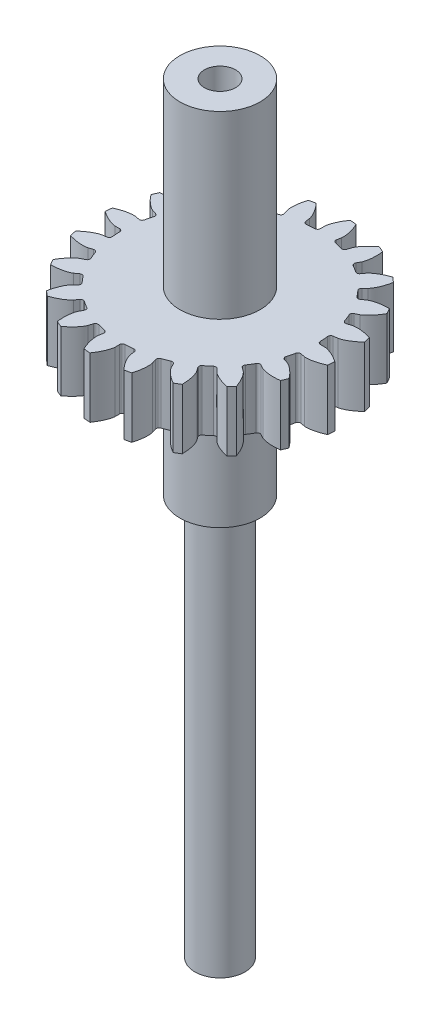
SolidWorks part; units mm, degrees
ref_plane "Front Plane" through (0, 0, 0) normal (0, 0, 1) x (1, 0, 0)
ref_plane "Top Plane" through (0, 0, 0) normal (0, 1, 0) x (1, 0, 0)
ref_plane "Right Plane" through (0, 0, 0) normal (1, 0, 0) x (0, 0, -1)
sketch "Sketch1" plane through (0, 0, 0) normal (0, 1, 0) x (1, 0, 0)
  circle A0 centre (0, 0) radius 2.5
  dimension "D1" = 5
extrude "BearingSection" add sketch "Sketch1" along normal mid plane 5
sketch "Sketch2" plane through (0, 2.5, 0) normal (0, 1, 0) x (1, 0, 0)
  circle A0 centre (0, 0) radius 4
  dimension "D1" = 8
extrude "Boss-Extrude2" add sketch "Sketch2" along normal blind 12
ref_plane "GearPlane" through (0, 14.5, 0) normal (0, 1, 0) x (1, 0, 0)
sketch "GearSketch" plane through (0, 14.5, 0) normal (0, 1, 0) x (1, 0, 0)
  line L122 (-9.8507, 1.7712) -> (-10.2891, 1.85)
  line L123 (-10.4541, 0) -> (-10.0086, 0)
  line L124 (-9.9159, -1.3596) -> (-10.3572, -1.4201)
  line L125 (-9.9424, -3.2305) -> (-9.5188, -3.0928)
  line L126 (-9.0104, -4.3572) -> (-9.4114, -4.5511)
  line L127 (-8.4575, -6.1448) -> (-8.0972, -5.8829)
  line L128 (-7.223, -6.9283) -> (-7.5444, -7.2367)
  line L129 (-6.1448, -8.4575) -> (-5.8829, -8.0972)
  line L130 (-4.7285, -8.8212) -> (-4.9389, -9.2138)
  line L131 (-3.2305, -9.9424) -> (-3.0928, -9.5188)
  line L132 (-1.7712, -9.8507) -> (-1.85, -10.2891)
  line L133 (0, -10.4541) -> (0, -10.0086)
  line L134 (1.3596, -9.9159) -> (1.4201, -10.3572)
  line L135 (3.2305, -9.9424) -> (3.0928, -9.5188)
  line L136 (4.3572, -9.0104) -> (4.5511, -9.4114)
  line L137 (6.1448, -8.4575) -> (5.8829, -8.0972)
  line L138 (6.9283, -7.223) -> (7.2367, -7.5444)
  line L139 (8.4575, -6.1448) -> (8.0972, -5.8829)
  line L140 (8.8212, -4.7285) -> (9.2138, -4.9389)
  line L141 (9.9424, -3.2305) -> (9.5188, -3.0928)
  line L142 (9.8507, -1.7712) -> (10.2891, -1.85)
  line L143 (10.4541, 0) -> (10.0086, 0)
  line L144 (9.9159, 1.3596) -> (10.3572, 1.4201)
  line L145 (9.9424, 3.2305) -> (9.5188, 3.0928)
  line L146 (9.0104, 4.3572) -> (9.4114, 4.5511)
  line L147 (8.4575, 6.1448) -> (8.0972, 5.8829)
  line L148 (7.223, 6.9283) -> (7.5444, 7.2367)
  line L149 (6.1448, 8.4575) -> (5.8829, 8.0972)
  line L150 (4.7285, 8.8212) -> (4.9389, 9.2138)
  line L151 (3.2305, 9.9424) -> (3.0928, 9.5188)
  line L152 (1.7712, 9.8507) -> (1.85, 10.2891)
  line L153 (0, 10.4541) -> (0, 10.0086)
  line L154 (-1.3596, 9.9159) -> (-1.4201, 10.3572)
  line L155 (-3.2305, 9.9424) -> (-3.0928, 9.5188)
  line L156 (-4.3572, 9.0104) -> (-4.5511, 9.4114)
  line L157 (-6.1448, 8.4575) -> (-5.8829, 8.0972)
  line L158 (-6.9283, 7.223) -> (-7.2367, 7.5444)
  line L159 (-8.4575, 6.1448) -> (-8.0972, 5.8829)
  line L160 (-8.8212, 4.7285) -> (-9.2138, 4.9389)
  line L161 (-9.9424, 3.2305) -> (-9.5188, 3.0928)
  arc A240 (-9.3379, 2.7498) -> (-9.5292, 1.9881) centre (0, 0) ccw
  arc A241 (-9.8507, 1.7712) -> (-9.5292, 1.9881) centre (-9.8015, 2.0449) ccw
  arc A242 (-12.1552, 1.4168) -> (-12.2141, 0.7565) centre (0, 0) ccw
  arc A243 (-9.7306, -0.2704) -> (-10.0086, 0) centre (-10.0086, -0.2781) ccw
  arc A244 (-9.7306, -0.2704) -> (-9.6772, -1.0539) centre (0, 0) ccw
  arc A245 (-9.9159, -1.3596) -> (-9.6772, -1.0539) centre (-9.9536, -1.084) ccw
  arc A246 (-11.9981, -2.4087) -> (-11.8501, -3.0549) centre (0, 0) ccw
  arc A247 (-9.1708, -3.2641) -> (-9.5188, -3.0928) centre (-9.4328, -3.3574) ccw
  arc A248 (-9.1708, -3.2641) -> (-8.8778, -3.9927) centre (0, 0) ccw
  arc A249 (-9.0104, -4.3572) -> (-8.8778, -3.9927) centre (-9.1315, -4.1068) ccw
  arc A250 (-10.6666, -5.9984) -> (-10.3261, -6.5672) centre (0, 0) ccw
  arc A251 (-7.7133, -5.9383) -> (-8.0972, -5.8829) centre (-7.9337, -6.1079) ccw
  arc A252 (-7.7133, -5.9383) -> (-7.2095, -6.5407) centre (0, 0) ccw
  arc A253 (-7.223, -6.9283) -> (-7.2095, -6.5407) centre (-7.4155, -6.7276) ccw
  arc A254 (-8.2909, -9.001) -> (-7.7913, -9.4367) centre (0, 0) ccw
  arc A255 (-5.5008, -8.0312) -> (-5.8829, -8.0972) centre (-5.6579, -8.2606) ccw
  arc A256 (-5.5008, -8.0312) -> (-4.8355, -8.4485) centre (0, 0) ccw
  arc A257 (-4.7285, -8.8212) -> (-4.8355, -8.4485) centre (-4.9736, -8.6898) ccw
  arc A258 (-5.1037, -11.1225) -> (-4.4939, -11.3825) centre (0, 0) ccw
  arc A259 (-2.7498, -9.3379) -> (-3.0928, -9.5188) centre (-2.8283, -9.6047) ccw
  arc A260 (-2.7498, -9.3379) -> (-1.9881, -9.5292) centre (0, 0) ccw
  arc A261 (-1.7712, -9.8507) -> (-1.9881, -9.5292) centre (-2.0449, -9.8015) ccw
  arc A262 (-1.4168, -12.1552) -> (-0.7565, -12.2141) centre (0, 0) ccw
  arc A263 (0.2704, -9.7306) -> (0, -10.0086) centre (0.2781, -10.0086) ccw
  arc A264 (0.2704, -9.7306) -> (1.0539, -9.6772) centre (0, 0) ccw
  arc A265 (1.3596, -9.9159) -> (1.0539, -9.6772) centre (1.084, -9.9536) ccw
  arc A266 (2.4087, -11.9981) -> (3.0549, -11.8501) centre (0, 0) ccw
  arc A267 (3.2641, -9.1708) -> (3.0928, -9.5188) centre (3.3574, -9.4328) ccw
  arc A268 (3.2641, -9.1708) -> (3.9927, -8.8778) centre (0, 0) ccw
  arc A269 (4.3572, -9.0104) -> (3.9927, -8.8778) centre (4.1068, -9.1315) ccw
  arc A270 (5.9984, -10.6666) -> (6.5672, -10.3261) centre (0, 0) ccw
  arc A271 (5.9383, -7.7133) -> (5.8829, -8.0972) centre (6.1079, -7.9337) ccw
  arc A272 (5.9383, -7.7133) -> (6.5407, -7.2095) centre (0, 0) ccw
  arc A273 (6.9283, -7.223) -> (6.5407, -7.2095) centre (6.7276, -7.4155) ccw
  arc A274 (9.001, -8.2909) -> (9.4367, -7.7913) centre (0, 0) ccw
  arc A275 (8.0312, -5.5008) -> (8.0972, -5.8829) centre (8.2606, -5.6579) ccw
  arc A276 (8.0312, -5.5008) -> (8.4485, -4.8355) centre (0, 0) ccw
  arc A277 (8.8212, -4.7285) -> (8.4485, -4.8355) centre (8.6898, -4.9736) ccw
  arc A278 (11.1225, -5.1037) -> (11.3825, -4.4939) centre (0, 0) ccw
  arc A279 (9.3379, -2.7498) -> (9.5188, -3.0928) centre (9.6047, -2.8283) ccw
  arc A280 (9.3379, -2.7498) -> (9.5292, -1.9881) centre (0, 0) ccw
  arc A281 (9.8507, -1.7712) -> (9.5292, -1.9881) centre (9.8015, -2.0449) ccw
  arc A282 (12.1552, -1.4168) -> (12.2141, -0.7565) centre (0, 0) ccw
  arc A283 (9.7306, 0.2704) -> (10.0086, 0) centre (10.0086, 0.2781) ccw
  arc A284 (9.7306, 0.2704) -> (9.6772, 1.0539) centre (0, 0) ccw
  arc A285 (9.9159, 1.3596) -> (9.6772, 1.0539) centre (9.9536, 1.084) ccw
  arc A286 (11.9981, 2.4087) -> (11.8501, 3.0549) centre (0, 0) ccw
  arc A287 (9.1708, 3.2641) -> (9.5188, 3.0928) centre (9.4328, 3.3574) ccw
  arc A288 (9.1708, 3.2641) -> (8.8778, 3.9927) centre (0, 0) ccw
  arc A289 (9.0104, 4.3572) -> (8.8778, 3.9927) centre (9.1315, 4.1068) ccw
  arc A290 (10.6666, 5.9984) -> (10.3261, 6.5672) centre (0, 0) ccw
  arc A291 (7.7133, 5.9383) -> (8.0972, 5.8829) centre (7.9337, 6.1079) ccw
  arc A292 (7.7133, 5.9383) -> (7.2095, 6.5407) centre (0, 0) ccw
  arc A293 (7.223, 6.9283) -> (7.2095, 6.5407) centre (7.4155, 6.7276) ccw
  arc A294 (8.2909, 9.001) -> (7.7913, 9.4367) centre (0, 0) ccw
  arc A295 (5.5008, 8.0312) -> (5.8829, 8.0972) centre (5.6579, 8.2606) ccw
  arc A296 (5.5008, 8.0312) -> (4.8355, 8.4485) centre (0, 0) ccw
  arc A297 (4.7285, 8.8212) -> (4.8355, 8.4485) centre (4.9736, 8.6898) ccw
  arc A298 (5.1037, 11.1225) -> (4.4939, 11.3825) centre (0, 0) ccw
  arc A299 (2.7498, 9.3379) -> (3.0928, 9.5188) centre (2.8283, 9.6047) ccw
  arc A300 (2.7498, 9.3379) -> (1.9881, 9.5292) centre (0, 0) ccw
  arc A301 (1.7712, 9.8507) -> (1.9881, 9.5292) centre (2.0449, 9.8015) ccw
  arc A302 (1.4168, 12.1552) -> (0.7565, 12.2141) centre (0, 0) ccw
  arc A303 (-0.2704, 9.7306) -> (0, 10.0086) centre (-0.2781, 10.0086) ccw
  arc A304 (-0.2704, 9.7306) -> (-1.0539, 9.6772) centre (0, 0) ccw
  arc A305 (-1.3596, 9.9159) -> (-1.0539, 9.6772) centre (-1.084, 9.9536) ccw
  arc A306 (-2.4087, 11.9981) -> (-3.0549, 11.8501) centre (0, 0) ccw
  arc A307 (-3.2641, 9.1708) -> (-3.0928, 9.5188) centre (-3.3574, 9.4328) ccw
  arc A308 (-3.2641, 9.1708) -> (-3.9927, 8.8778) centre (0, 0) ccw
  arc A309 (-4.3572, 9.0104) -> (-3.9927, 8.8778) centre (-4.1068, 9.1315) ccw
  arc A310 (-5.9984, 10.6666) -> (-6.5672, 10.3261) centre (0, 0) ccw
  arc A311 (-5.9383, 7.7133) -> (-5.8829, 8.0972) centre (-6.1079, 7.9337) ccw
  arc A312 (-5.9383, 7.7133) -> (-6.5407, 7.2095) centre (0, 0) ccw
  arc A313 (-6.9283, 7.223) -> (-6.5407, 7.2095) centre (-6.7276, 7.4155) ccw
  arc A314 (-9.001, 8.2909) -> (-9.4367, 7.7913) centre (0, 0) ccw
  arc A315 (-8.0312, 5.5008) -> (-8.0972, 5.8829) centre (-8.2606, 5.6579) ccw
  arc A316 (-8.0312, 5.5008) -> (-8.4485, 4.8355) centre (0, 0) ccw
  arc A317 (-8.8212, 4.7285) -> (-8.4485, 4.8355) centre (-8.6898, 4.9736) ccw
  arc A318 (-11.1225, 5.1037) -> (-11.3825, 4.4939) centre (0, 0) ccw
  arc A319 (-9.3379, 2.7498) -> (-9.5188, 3.0928) centre (-9.6047, 2.8283) ccw
  spline S121 degree 4 poles (-10.2891, 1.85) (-10.2967, 1.8512) (-10.3182, 1.8541) (-10.3591, 1.8575) (-10.4261, 1.8604) (-10.5116, 1.8598) (-10.6222, 1.8543) (-10.7524, 1.8417) (-10.8951, 1.8213) (-11.0496, 1.7923) (-11.203, 1.7573) (-11.3551, 1.7168) (-11.5057, 1.6713) (-11.6868, 1.6104) (-11.8683, 1.5419) (-12.0112, 1.4818) (-12.1166, 1.4346) (-12.1552, 1.4168) knots 0 0 0 0 0 0.005377 0.015084 0.028532 0.04661 0.064855 0.092111 0.119476 0.146842 0.174209 0.201575 0.228941 0.256307 0.307035 0.336625 0.336625 0.336625 0.336625 0.336625
  spline S122 degree 4 poles (-12.2141, 0.7565) (-12.1792, 0.7322) (-12.0839, 0.6671) (-11.9538, 0.5827) (-11.7874, 0.4832) (-11.6199, 0.3911) (-11.4797, 0.3198) (-11.3372, 0.2529) (-11.1924, 0.1913) (-11.0454, 0.1354) (-10.9086, 0.0902) (-10.7827, 0.0547) (-10.6748, 0.0297) (-10.5907, 0.014) (-10.5243, 0.005) (-10.4835, 0.0011) (-10.4618, 0.0002) (-10.4541, 0) knots 0 0 0 0 0 0.02959 0.080317 0.107684 0.13505 0.162416 0.189782 0.217148 0.244514 0.27177 0.290014 0.308093 0.321541 0.331248 0.336625 0.336625 0.336625 0.336625 0.336625
  spline S123 degree 4 poles (-10.3572, -1.4201) (-10.3648, -1.4213) (-10.3861, -1.4252) (-10.4261, -1.4345) (-10.4907, -1.4525) (-10.5718, -1.4795) (-10.6753, -1.5189) (-10.7952, -1.5711) (-10.9246, -1.6346) (-11.0627, -1.7099) (-11.1977, -1.7906) (-11.3299, -1.8762) (-11.4591, -1.9659) (-11.6125, -2.0799) (-11.7639, -2.2011) (-11.8813, -2.3024) (-11.9668, -2.3799) (-11.9981, -2.4087) knots 0 0 0 0 0 0.005377 0.015084 0.028532 0.04661 0.064855 0.092111 0.119476 0.146842 0.174209 0.201575 0.228941 0.256307 0.307035 0.336625 0.336625 0.336625 0.336625 0.336625
  spline S124 degree 4 poles (-11.8501, -3.0549) (-11.8094, -3.0672) (-11.6986, -3.0997) (-11.5488, -3.1397) (-11.3598, -3.183) (-11.172, -3.2188) (-11.0167, -3.2433) (-10.8605, -3.2628) (-10.7037, -3.2767) (-10.5467, -3.2844) (-10.4025, -3.2852) (-10.2719, -3.28) (-10.1615, -3.2705) (-10.0767, -3.2594) (-10.0108, -3.2475) (-9.9707, -3.2385) (-9.9498, -3.2327) (-9.9424, -3.2305) knots 0 0 0 0 0 0.02959 0.080317 0.107684 0.13505 0.162416 0.189782 0.217148 0.244514 0.27177 0.290014 0.308093 0.321541 0.331248 0.336625 0.336625 0.336625 0.336625 0.336625
  spline S125 degree 4 poles (-9.4114, -4.5511) (-9.4183, -4.5546) (-9.4374, -4.5649) (-9.4725, -4.5861) (-9.5284, -4.6232) (-9.5972, -4.6739) (-9.6835, -4.7434) (-9.7814, -4.8302) (-9.8848, -4.9305) (-9.9928, -5.0448) (-10.0964, -5.1633) (-10.1956, -5.2855) (-10.2907, -5.4108) (-10.4014, -5.5665) (-10.5079, -5.7286) (-10.5883, -5.8612) (-10.6457, -5.9613) (-10.6666, -5.9984) knots 0 0 0 0 0 0.005377 0.015084 0.028532 0.04661 0.064855 0.092111 0.119476 0.146842 0.174209 0.201575 0.228941 0.256307 0.307035 0.336625 0.336625 0.336625 0.336625 0.336625
  spline S126 degree 4 poles (-10.3261, -6.5672) (-10.2836, -6.5664) (-10.1682, -6.5631) (-10.0134, -6.5549) (-9.8202, -6.5375) (-9.6306, -6.5136) (-9.4752, -6.4889) (-9.3206, -6.4592) (-9.1673, -6.4239) (-9.0155, -6.3828) (-8.8782, -6.3389) (-8.7555, -6.2937) (-8.6536, -6.2505) (-8.5763, -6.2137) (-8.5173, -6.182) (-8.482, -6.1611) (-8.4639, -6.1492) (-8.4575, -6.1448) knots 0 0 0 0 0 0.02959 0.080317 0.107684 0.13505 0.162416 0.189782 0.217148 0.244514 0.27177 0.290014 0.308093 0.321541 0.331248 0.336625 0.336625 0.336625 0.336625 0.336625
  spline S127 degree 4 poles (-7.5444, -7.2367) (-7.5499, -7.2421) (-7.5649, -7.2578) (-7.5917, -7.2889) (-7.6334, -7.3414) (-7.6832, -7.4109) (-7.7437, -7.5036) (-7.81, -7.6164) (-7.8774, -7.7437) (-7.9448, -7.8858) (-8.0067, -8.0305) (-8.0633, -8.1774) (-8.115, -8.3259) (-8.1722, -8.5083) (-8.2234, -8.6954) (-8.2589, -8.8463) (-8.2825, -8.9593) (-8.2909, -9.001) knots 0 0 0 0 0 0.005377 0.015084 0.028532 0.04661 0.064855 0.092111 0.119476 0.146842 0.174209 0.201575 0.228941 0.256307 0.307035 0.336625 0.336625 0.336625 0.336625 0.336625
  spline S128 degree 4 poles (-7.7913, -9.4367) (-7.7511, -9.4228) (-7.6424, -9.384) (-7.4977, -9.3283) (-7.3193, -9.2522) (-7.1464, -9.1708) (-7.0063, -9.0993) (-6.8685, -9.0233) (-6.7335, -8.9424) (-6.6019, -8.8563) (-6.4849, -8.7722) (-6.3822, -8.6912) (-6.2985, -8.6186) (-6.2364, -8.5598) (-6.1901, -8.5115) (-6.1629, -8.4806) (-6.1494, -8.4637) (-6.1448, -8.4575) knots 0 0 0 0 0 0.02959 0.080317 0.107684 0.13505 0.162416 0.189782 0.217148 0.244514 0.27177 0.290014 0.308093 0.321541 0.331248 0.336625 0.336625 0.336625 0.336625 0.336625
  spline S129 degree 4 poles (-4.9389, -9.2138) (-4.9424, -9.2207) (-4.9518, -9.2403) (-4.9678, -9.2781) (-4.9911, -9.3409) (-5.017, -9.4224) (-5.046, -9.5293) (-5.0742, -9.657) (-5.099, -9.799) (-5.1191, -9.9549) (-5.1332, -10.1117) (-5.1417, -10.2689) (-5.145, -10.4261) (-5.143, -10.6172) (-5.1339, -10.8109) (-5.121, -10.9654) (-5.1086, -11.0802) (-5.1037, -11.1225) knots 0 0 0 0 0 0.005377 0.015084 0.028532 0.04661 0.064855 0.092111 0.119476 0.146842 0.174209 0.201575 0.228941 0.256307 0.307035 0.336625 0.336625 0.336625 0.336625 0.336625
  spline S130 degree 4 poles (-4.4939, -11.3825) (-4.46, -11.3568) (-4.3686, -11.2863) (-4.2481, -11.1887) (-4.102, -11.0611) (-3.9627, -10.9303) (-3.8515, -10.8191) (-3.7439, -10.7041) (-3.6406, -10.5855) (-3.542, -10.463) (-3.4567, -10.3468) (-3.3841, -10.2381) (-3.3269, -10.1432) (-3.286, -10.068) (-3.2569, -10.0077) (-3.2406, -9.97) (-3.233, -9.9497) (-3.2305, -9.9424) knots 0 0 0 0 0 0.02959 0.080317 0.107684 0.13505 0.162416 0.189782 0.217148 0.244514 0.27177 0.290014 0.308093 0.321541 0.331248 0.336625 0.336625 0.336625 0.336625 0.336625
  spline S131 degree 4 poles (-1.85, -10.2891) (-1.8512, -10.2967) (-1.8541, -10.3182) (-1.8575, -10.3591) (-1.8604, -10.4261) (-1.8598, -10.5116) (-1.8543, -10.6222) (-1.8417, -10.7524) (-1.8213, -10.8951) (-1.7923, -11.0496) (-1.7573, -11.203) (-1.7168, -11.3551) (-1.6713, -11.5057) (-1.6104, -11.6868) (-1.5419, -11.8683) (-1.4818, -12.0112) (-1.4346, -12.1166) (-1.4168, -12.1552) knots 0 0 0 0 0 0.005377 0.015084 0.028532 0.04661 0.064855 0.092111 0.119476 0.146842 0.174209 0.201575 0.228941 0.256307 0.307035 0.336625 0.336625 0.336625 0.336625 0.336625
  spline S132 degree 4 poles (-0.7565, -12.2141) (-0.7322, -12.1792) (-0.6671, -12.0839) (-0.5827, -11.9538) (-0.4832, -11.7874) (-0.3911, -11.6199) (-0.3198, -11.4797) (-0.2529, -11.3372) (-0.1913, -11.1924) (-0.1354, -11.0454) (-0.0902, -10.9086) (-0.0547, -10.7827) (-0.0297, -10.6748) (-0.014, -10.5907) (-0.005, -10.5243) (-0.0011, -10.4835) (-0.0002, -10.4618) (0, -10.4541) knots 0 0 0 0 0 0.02959 0.080317 0.107684 0.13505 0.162416 0.189782 0.217148 0.244514 0.27177 0.290014 0.308093 0.321541 0.331248 0.336625 0.336625 0.336625 0.336625 0.336625
  spline S133 degree 4 poles (1.4201, -10.3572) (1.4213, -10.3648) (1.4252, -10.3861) (1.4345, -10.4261) (1.4525, -10.4907) (1.4795, -10.5718) (1.5189, -10.6753) (1.5711, -10.7952) (1.6346, -10.9246) (1.7099, -11.0627) (1.7906, -11.1977) (1.8762, -11.3299) (1.9659, -11.4591) (2.0799, -11.6125) (2.2011, -11.7639) (2.3024, -11.8813) (2.3799, -11.9668) (2.4087, -11.9981) knots 0 0 0 0 0 0.005377 0.015084 0.028532 0.04661 0.064855 0.092111 0.119476 0.146842 0.174209 0.201575 0.228941 0.256307 0.307035 0.336625 0.336625 0.336625 0.336625 0.336625
  spline S134 degree 4 poles (3.0549, -11.8501) (3.0672, -11.8094) (3.0997, -11.6986) (3.1397, -11.5488) (3.183, -11.3598) (3.2188, -11.172) (3.2433, -11.0167) (3.2628, -10.8605) (3.2767, -10.7037) (3.2844, -10.5467) (3.2852, -10.4025) (3.28, -10.2719) (3.2705, -10.1615) (3.2594, -10.0767) (3.2475, -10.0108) (3.2385, -9.9707) (3.2327, -9.9498) (3.2305, -9.9424) knots 0 0 0 0 0 0.02959 0.080317 0.107684 0.13505 0.162416 0.189782 0.217148 0.244514 0.27177 0.290014 0.308093 0.321541 0.331248 0.336625 0.336625 0.336625 0.336625 0.336625
  spline S135 degree 4 poles (4.5511, -9.4114) (4.5546, -9.4183) (4.5649, -9.4374) (4.5861, -9.4725) (4.6232, -9.5284) (4.6739, -9.5972) (4.7434, -9.6835) (4.8302, -9.7814) (4.9305, -9.8848) (5.0448, -9.9928) (5.1633, -10.0964) (5.2855, -10.1956) (5.4108, -10.2907) (5.5665, -10.4014) (5.7286, -10.5079) (5.8612, -10.5883) (5.9613, -10.6457) (5.9984, -10.6666) knots 0 0 0 0 0 0.005377 0.015084 0.028532 0.04661 0.064855 0.092111 0.119476 0.146842 0.174209 0.201575 0.228941 0.256307 0.307035 0.336625 0.336625 0.336625 0.336625 0.336625
  spline S136 degree 4 poles (6.5672, -10.3261) (6.5664, -10.2836) (6.5631, -10.1682) (6.5549, -10.0134) (6.5375, -9.8202) (6.5136, -9.6306) (6.4889, -9.4752) (6.4592, -9.3206) (6.4239, -9.1673) (6.3828, -9.0155) (6.3389, -8.8782) (6.2937, -8.7555) (6.2505, -8.6536) (6.2137, -8.5763) (6.182, -8.5173) (6.1611, -8.482) (6.1492, -8.4639) (6.1448, -8.4575) knots 0 0 0 0 0 0.02959 0.080317 0.107684 0.13505 0.162416 0.189782 0.217148 0.244514 0.27177 0.290014 0.308093 0.321541 0.331248 0.336625 0.336625 0.336625 0.336625 0.336625
  spline S137 degree 4 poles (7.2367, -7.5444) (7.2421, -7.5499) (7.2578, -7.5649) (7.2889, -7.5917) (7.3414, -7.6334) (7.4109, -7.6832) (7.5036, -7.7437) (7.6164, -7.81) (7.7437, -7.8774) (7.8858, -7.9448) (8.0305, -8.0067) (8.1774, -8.0633) (8.3259, -8.115) (8.5083, -8.1722) (8.6954, -8.2234) (8.8463, -8.2589) (8.9593, -8.2825) (9.001, -8.2909) knots 0 0 0 0 0 0.005377 0.015084 0.028532 0.04661 0.064855 0.092111 0.119476 0.146842 0.174209 0.201575 0.228941 0.256307 0.307035 0.336625 0.336625 0.336625 0.336625 0.336625
  spline S138 degree 4 poles (9.4367, -7.7913) (9.4228, -7.7511) (9.384, -7.6424) (9.3283, -7.4977) (9.2522, -7.3193) (9.1708, -7.1464) (9.0993, -7.0063) (9.0233, -6.8685) (8.9424, -6.7335) (8.8563, -6.6019) (8.7722, -6.4849) (8.6912, -6.3822) (8.6186, -6.2985) (8.5598, -6.2364) (8.5115, -6.1901) (8.4806, -6.1629) (8.4637, -6.1494) (8.4575, -6.1448) knots 0 0 0 0 0 0.02959 0.080317 0.107684 0.13505 0.162416 0.189782 0.217148 0.244514 0.27177 0.290014 0.308093 0.321541 0.331248 0.336625 0.336625 0.336625 0.336625 0.336625
  spline S139 degree 4 poles (9.2138, -4.9389) (9.2207, -4.9424) (9.2403, -4.9518) (9.2781, -4.9678) (9.3409, -4.9911) (9.4224, -5.017) (9.5293, -5.046) (9.657, -5.0742) (9.799, -5.099) (9.9549, -5.1191) (10.1117, -5.1332) (10.2689, -5.1417) (10.4261, -5.145) (10.6172, -5.143) (10.8109, -5.1339) (10.9654, -5.121) (11.0802, -5.1086) (11.1225, -5.1037) knots 0 0 0 0 0 0.005377 0.015084 0.028532 0.04661 0.064855 0.092111 0.119476 0.146842 0.174209 0.201575 0.228941 0.256307 0.307035 0.336625 0.336625 0.336625 0.336625 0.336625
  spline S140 degree 4 poles (11.3825, -4.4939) (11.3568, -4.46) (11.2863, -4.3686) (11.1887, -4.2481) (11.0611, -4.102) (10.9303, -3.9627) (10.8191, -3.8515) (10.7041, -3.7439) (10.5855, -3.6406) (10.463, -3.542) (10.3468, -3.4567) (10.2381, -3.3841) (10.1432, -3.3269) (10.068, -3.286) (10.0077, -3.2569) (9.97, -3.2406) (9.9497, -3.233) (9.9424, -3.2305) knots 0 0 0 0 0 0.02959 0.080317 0.107684 0.13505 0.162416 0.189782 0.217148 0.244514 0.27177 0.290014 0.308093 0.321541 0.331248 0.336625 0.336625 0.336625 0.336625 0.336625
  spline S141 degree 4 poles (10.2891, -1.85) (10.2967, -1.8512) (10.3182, -1.8541) (10.3591, -1.8575) (10.4261, -1.8604) (10.5116, -1.8598) (10.6222, -1.8543) (10.7524, -1.8417) (10.8951, -1.8213) (11.0496, -1.7923) (11.203, -1.7573) (11.3551, -1.7168) (11.5057, -1.6713) (11.6868, -1.6104) (11.8683, -1.5419) (12.0112, -1.4818) (12.1166, -1.4346) (12.1552, -1.4168) knots 0 0 0 0 0 0.005377 0.015084 0.028532 0.04661 0.064855 0.092111 0.119476 0.146842 0.174209 0.201575 0.228941 0.256307 0.307035 0.336625 0.336625 0.336625 0.336625 0.336625
  spline S142 degree 4 poles (12.2141, -0.7565) (12.1792, -0.7322) (12.0839, -0.6671) (11.9538, -0.5827) (11.7874, -0.4832) (11.6199, -0.3911) (11.4797, -0.3198) (11.3372, -0.2529) (11.1924, -0.1913) (11.0454, -0.1354) (10.9086, -0.0902) (10.7827, -0.0547) (10.6748, -0.0297) (10.5907, -0.014) (10.5243, -0.005) (10.4835, -0.0011) (10.4618, -0.0002) (10.4541, 0) knots 0 0 0 0 0 0.02959 0.080317 0.107684 0.13505 0.162416 0.189782 0.217148 0.244514 0.27177 0.290014 0.308093 0.321541 0.331248 0.336625 0.336625 0.336625 0.336625 0.336625
  spline S143 degree 4 poles (10.3572, 1.4201) (10.3648, 1.4213) (10.3861, 1.4252) (10.4261, 1.4345) (10.4907, 1.4525) (10.5718, 1.4795) (10.6753, 1.5189) (10.7952, 1.5711) (10.9246, 1.6346) (11.0627, 1.7099) (11.1977, 1.7906) (11.3299, 1.8762) (11.4591, 1.9659) (11.6125, 2.0799) (11.7639, 2.2011) (11.8813, 2.3024) (11.9668, 2.3799) (11.9981, 2.4087) knots 0 0 0 0 0 0.005377 0.015084 0.028532 0.04661 0.064855 0.092111 0.119476 0.146842 0.174209 0.201575 0.228941 0.256307 0.307035 0.336625 0.336625 0.336625 0.336625 0.336625
  spline S144 degree 4 poles (11.8501, 3.0549) (11.8094, 3.0672) (11.6986, 3.0997) (11.5488, 3.1397) (11.3598, 3.183) (11.172, 3.2188) (11.0167, 3.2433) (10.8605, 3.2628) (10.7037, 3.2767) (10.5467, 3.2844) (10.4025, 3.2852) (10.2719, 3.28) (10.1615, 3.2705) (10.0767, 3.2594) (10.0108, 3.2475) (9.9707, 3.2385) (9.9498, 3.2327) (9.9424, 3.2305) knots 0 0 0 0 0 0.02959 0.080317 0.107684 0.13505 0.162416 0.189782 0.217148 0.244514 0.27177 0.290014 0.308093 0.321541 0.331248 0.336625 0.336625 0.336625 0.336625 0.336625
  spline S145 degree 4 poles (9.4114, 4.5511) (9.4183, 4.5546) (9.4374, 4.5649) (9.4725, 4.5861) (9.5284, 4.6232) (9.5972, 4.6739) (9.6835, 4.7434) (9.7814, 4.8302) (9.8848, 4.9305) (9.9928, 5.0448) (10.0964, 5.1633) (10.1956, 5.2855) (10.2907, 5.4108) (10.4014, 5.5665) (10.5079, 5.7286) (10.5883, 5.8612) (10.6457, 5.9613) (10.6666, 5.9984) knots 0 0 0 0 0 0.005377 0.015084 0.028532 0.04661 0.064855 0.092111 0.119476 0.146842 0.174209 0.201575 0.228941 0.256307 0.307035 0.336625 0.336625 0.336625 0.336625 0.336625
  spline S146 degree 4 poles (10.3261, 6.5672) (10.2836, 6.5664) (10.1682, 6.5631) (10.0134, 6.5549) (9.8202, 6.5375) (9.6306, 6.5136) (9.4752, 6.4889) (9.3206, 6.4592) (9.1673, 6.4239) (9.0155, 6.3828) (8.8782, 6.3389) (8.7555, 6.2937) (8.6536, 6.2505) (8.5763, 6.2137) (8.5173, 6.182) (8.482, 6.1611) (8.4639, 6.1492) (8.4575, 6.1448) knots 0 0 0 0 0 0.02959 0.080317 0.107684 0.13505 0.162416 0.189782 0.217148 0.244514 0.27177 0.290014 0.308093 0.321541 0.331248 0.336625 0.336625 0.336625 0.336625 0.336625
  spline S147 degree 4 poles (7.5444, 7.2367) (7.5499, 7.2421) (7.5649, 7.2578) (7.5917, 7.2889) (7.6334, 7.3414) (7.6832, 7.4109) (7.7437, 7.5036) (7.81, 7.6164) (7.8774, 7.7437) (7.9448, 7.8858) (8.0067, 8.0305) (8.0633, 8.1774) (8.115, 8.3259) (8.1722, 8.5083) (8.2234, 8.6954) (8.2589, 8.8463) (8.2825, 8.9593) (8.2909, 9.001) knots 0 0 0 0 0 0.005377 0.015084 0.028532 0.04661 0.064855 0.092111 0.119476 0.146842 0.174209 0.201575 0.228941 0.256307 0.307035 0.336625 0.336625 0.336625 0.336625 0.336625
  spline S148 degree 4 poles (7.7913, 9.4367) (7.7511, 9.4228) (7.6424, 9.384) (7.4977, 9.3283) (7.3193, 9.2522) (7.1464, 9.1708) (7.0063, 9.0993) (6.8685, 9.0233) (6.7335, 8.9424) (6.6019, 8.8563) (6.4849, 8.7722) (6.3822, 8.6912) (6.2985, 8.6186) (6.2364, 8.5598) (6.1901, 8.5115) (6.1629, 8.4806) (6.1494, 8.4637) (6.1448, 8.4575) knots 0 0 0 0 0 0.02959 0.080317 0.107684 0.13505 0.162416 0.189782 0.217148 0.244514 0.27177 0.290014 0.308093 0.321541 0.331248 0.336625 0.336625 0.336625 0.336625 0.336625
  spline S149 degree 4 poles (4.9389, 9.2138) (4.9424, 9.2207) (4.9518, 9.2403) (4.9678, 9.2781) (4.9911, 9.3409) (5.017, 9.4224) (5.046, 9.5293) (5.0742, 9.657) (5.099, 9.799) (5.1191, 9.9549) (5.1332, 10.1117) (5.1417, 10.2689) (5.145, 10.4261) (5.143, 10.6172) (5.1339, 10.8109) (5.121, 10.9654) (5.1086, 11.0802) (5.1037, 11.1225) knots 0 0 0 0 0 0.005377 0.015084 0.028532 0.04661 0.064855 0.092111 0.119476 0.146842 0.174209 0.201575 0.228941 0.256307 0.307035 0.336625 0.336625 0.336625 0.336625 0.336625
  spline S150 degree 4 poles (4.4939, 11.3825) (4.46, 11.3568) (4.3686, 11.2863) (4.2481, 11.1887) (4.102, 11.0611) (3.9627, 10.9303) (3.8515, 10.8191) (3.7439, 10.7041) (3.6406, 10.5855) (3.542, 10.463) (3.4567, 10.3468) (3.3841, 10.2381) (3.3269, 10.1432) (3.286, 10.068) (3.2569, 10.0077) (3.2406, 9.97) (3.233, 9.9497) (3.2305, 9.9424) knots 0 0 0 0 0 0.02959 0.080317 0.107684 0.13505 0.162416 0.189782 0.217148 0.244514 0.27177 0.290014 0.308093 0.321541 0.331248 0.336625 0.336625 0.336625 0.336625 0.336625
  spline S151 degree 4 poles (1.85, 10.2891) (1.8512, 10.2967) (1.8541, 10.3182) (1.8575, 10.3591) (1.8604, 10.4261) (1.8598, 10.5116) (1.8543, 10.6222) (1.8417, 10.7524) (1.8213, 10.8951) (1.7923, 11.0496) (1.7573, 11.203) (1.7168, 11.3551) (1.6713, 11.5057) (1.6104, 11.6868) (1.5419, 11.8683) (1.4818, 12.0112) (1.4346, 12.1166) (1.4168, 12.1552) knots 0 0 0 0 0 0.005377 0.015084 0.028532 0.04661 0.064855 0.092111 0.119476 0.146842 0.174209 0.201575 0.228941 0.256307 0.307035 0.336625 0.336625 0.336625 0.336625 0.336625
  spline S152 degree 4 poles (0.7565, 12.2141) (0.7322, 12.1792) (0.6671, 12.0839) (0.5827, 11.9538) (0.4832, 11.7874) (0.3911, 11.6199) (0.3198, 11.4797) (0.2529, 11.3372) (0.1913, 11.1924) (0.1354, 11.0454) (0.0902, 10.9086) (0.0547, 10.7827) (0.0297, 10.6748) (0.014, 10.5907) (0.005, 10.5243) (0.0011, 10.4835) (0.0002, 10.4618) (0, 10.4541) knots 0 0 0 0 0 0.02959 0.080317 0.107684 0.13505 0.162416 0.189782 0.217148 0.244514 0.27177 0.290014 0.308093 0.321541 0.331248 0.336625 0.336625 0.336625 0.336625 0.336625
  spline S153 degree 4 poles (-1.4201, 10.3572) (-1.4213, 10.3648) (-1.4252, 10.3861) (-1.4345, 10.4261) (-1.4525, 10.4907) (-1.4795, 10.5718) (-1.5189, 10.6753) (-1.5711, 10.7952) (-1.6346, 10.9246) (-1.7099, 11.0627) (-1.7906, 11.1977) (-1.8762, 11.3299) (-1.9659, 11.4591) (-2.0799, 11.6125) (-2.2011, 11.7639) (-2.3024, 11.8813) (-2.3799, 11.9668) (-2.4087, 11.9981) knots 0 0 0 0 0 0.005377 0.015084 0.028532 0.04661 0.064855 0.092111 0.119476 0.146842 0.174209 0.201575 0.228941 0.256307 0.307035 0.336625 0.336625 0.336625 0.336625 0.336625
  spline S154 degree 4 poles (-3.0549, 11.8501) (-3.0672, 11.8094) (-3.0997, 11.6986) (-3.1397, 11.5488) (-3.183, 11.3598) (-3.2188, 11.172) (-3.2433, 11.0167) (-3.2628, 10.8605) (-3.2767, 10.7037) (-3.2844, 10.5467) (-3.2852, 10.4025) (-3.28, 10.2719) (-3.2705, 10.1615) (-3.2594, 10.0767) (-3.2475, 10.0108) (-3.2385, 9.9707) (-3.2327, 9.9498) (-3.2305, 9.9424) knots 0 0 0 0 0 0.02959 0.080317 0.107684 0.13505 0.162416 0.189782 0.217148 0.244514 0.27177 0.290014 0.308093 0.321541 0.331248 0.336625 0.336625 0.336625 0.336625 0.336625
  spline S155 degree 4 poles (-4.5511, 9.4114) (-4.5546, 9.4183) (-4.5649, 9.4374) (-4.5861, 9.4725) (-4.6232, 9.5284) (-4.6739, 9.5972) (-4.7434, 9.6835) (-4.8302, 9.7814) (-4.9305, 9.8848) (-5.0448, 9.9928) (-5.1633, 10.0964) (-5.2855, 10.1956) (-5.4108, 10.2907) (-5.5665, 10.4014) (-5.7286, 10.5079) (-5.8612, 10.5883) (-5.9613, 10.6457) (-5.9984, 10.6666) knots 0 0 0 0 0 0.005377 0.015084 0.028532 0.04661 0.064855 0.092111 0.119476 0.146842 0.174209 0.201575 0.228941 0.256307 0.307035 0.336625 0.336625 0.336625 0.336625 0.336625
  spline S156 degree 4 poles (-6.5672, 10.3261) (-6.5664, 10.2836) (-6.5631, 10.1682) (-6.5549, 10.0134) (-6.5375, 9.8202) (-6.5136, 9.6306) (-6.4889, 9.4752) (-6.4592, 9.3206) (-6.4239, 9.1673) (-6.3828, 9.0155) (-6.3389, 8.8782) (-6.2937, 8.7555) (-6.2505, 8.6536) (-6.2137, 8.5763) (-6.182, 8.5173) (-6.1611, 8.482) (-6.1492, 8.4639) (-6.1448, 8.4575) knots 0 0 0 0 0 0.02959 0.080317 0.107684 0.13505 0.162416 0.189782 0.217148 0.244514 0.27177 0.290014 0.308093 0.321541 0.331248 0.336625 0.336625 0.336625 0.336625 0.336625
  spline S157 degree 4 poles (-7.2367, 7.5444) (-7.2421, 7.5499) (-7.2578, 7.5649) (-7.2889, 7.5917) (-7.3414, 7.6334) (-7.4109, 7.6832) (-7.5036, 7.7437) (-7.6164, 7.81) (-7.7437, 7.8774) (-7.8858, 7.9448) (-8.0305, 8.0067) (-8.1774, 8.0633) (-8.3259, 8.115) (-8.5083, 8.1722) (-8.6954, 8.2234) (-8.8463, 8.2589) (-8.9593, 8.2825) (-9.001, 8.2909) knots 0 0 0 0 0 0.005377 0.015084 0.028532 0.04661 0.064855 0.092111 0.119476 0.146842 0.174209 0.201575 0.228941 0.256307 0.307035 0.336625 0.336625 0.336625 0.336625 0.336625
  spline S158 degree 4 poles (-9.4367, 7.7913) (-9.4228, 7.7511) (-9.384, 7.6424) (-9.3283, 7.4977) (-9.2522, 7.3193) (-9.1708, 7.1464) (-9.0993, 7.0063) (-9.0233, 6.8685) (-8.9424, 6.7335) (-8.8563, 6.6019) (-8.7722, 6.4849) (-8.6912, 6.3822) (-8.6186, 6.2985) (-8.5598, 6.2364) (-8.5115, 6.1901) (-8.4806, 6.1629) (-8.4637, 6.1494) (-8.4575, 6.1448) knots 0 0 0 0 0 0.02959 0.080317 0.107684 0.13505 0.162416 0.189782 0.217148 0.244514 0.27177 0.290014 0.308093 0.321541 0.331248 0.336625 0.336625 0.336625 0.336625 0.336625
  spline S159 degree 4 poles (-9.2138, 4.9389) (-9.2207, 4.9424) (-9.2403, 4.9518) (-9.2781, 4.9678) (-9.3409, 4.9911) (-9.4224, 5.017) (-9.5293, 5.046) (-9.657, 5.0742) (-9.799, 5.099) (-9.9549, 5.1191) (-10.1117, 5.1332) (-10.2689, 5.1417) (-10.4261, 5.145) (-10.6172, 5.143) (-10.8109, 5.1339) (-10.9654, 5.121) (-11.0802, 5.1086) (-11.1225, 5.1037) knots 0 0 0 0 0 0.005377 0.015084 0.028532 0.04661 0.064855 0.092111 0.119476 0.146842 0.174209 0.201575 0.228941 0.256307 0.307035 0.336625 0.336625 0.336625 0.336625 0.336625
  spline S160 degree 4 poles (-11.3825, 4.4939) (-11.3568, 4.46) (-11.2863, 4.3686) (-11.1887, 4.2481) (-11.0611, 4.102) (-10.9303, 3.9627) (-10.8191, 3.8515) (-10.7041, 3.7439) (-10.5855, 3.6406) (-10.463, 3.542) (-10.3468, 3.4567) (-10.2381, 3.3841) (-10.1432, 3.3269) (-10.068, 3.286) (-10.0077, 3.2569) (-9.97, 3.2406) (-9.9497, 3.233) (-9.9424, 3.2305) knots 0 0 0 0 0 0.02959 0.080317 0.107684 0.13505 0.162416 0.189782 0.217148 0.244514 0.27177 0.290014 0.308093 0.321541 0.331248 0.336625 0.336625 0.336625 0.336625 0.336625
extrude "Boss-Extrude3" add sketch "GearSketch" along normal blind 6
sketch "Sketch7" plane through (0, 20.5, 0) normal (0, 1, 0) x (1, 0, 0)
  circle A0 centre (0, 0) radius 4
  dimension "D1" = 8
extrude "Boss-Extrude4" add sketch "Sketch7" along normal blind 17.95
sketch "Sketch8" plane through (0, 38.45, 0) normal (0, 1, 0) x (1, 0, 0)
  circle A0 centre (0, 0) radius 1.55
  dimension "D1" = 3.1
extrude "Cut-Extrude1" cut sketch "Sketch8" against normal offset from surface (18.95 mm away) 17 up to face at (0, 2.5, 2.5)
sketch "Sketch9" plane through (0, -2.5, 0) normal (0, -1, 0) x (1, 0, 0)
  circle A0 centre (0, 0) radius 2.5
  dimension "D1" = 5
extrude "Boss-Extrude5" add sketch "Sketch9" along normal blind 34.95
sketch "Sketch10" plane through (0, -37.45, 0) normal (0, -1, 0) x (1, 0, 0)
  circle A0 centre (0, 0) radius 1.55
  dimension "D1" = 3.1
extrude "Cut-Extrude2" cut sketch "Sketch10" against normal blind 17
